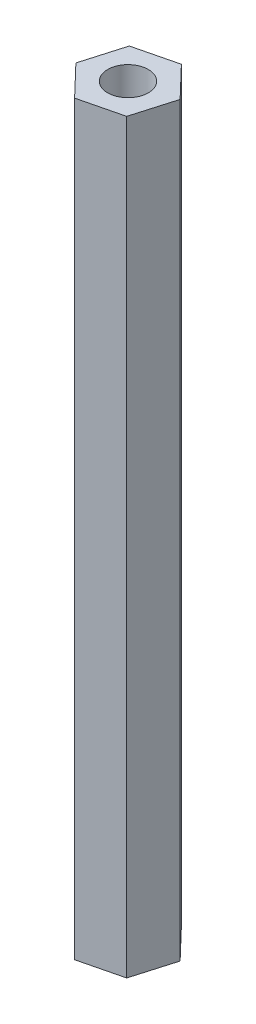
SolidWorks part; units mm, degrees
ref_plane "Front Plane" through (0, 0, 0) normal (0, 0, 1) x (1, 0, 0)
ref_plane "Top Plane" through (0, 0, 0) normal (0, 1, 0) x (1, 0, 0)
ref_plane "Right Plane" through (0, 0, 0) normal (1, 0, 0) x (0, 0, -1)
sketch "Sketch1" plane through (0, 0, 0) normal (0, 1, 0) x (1, 0, 0)
  line L1 (-2.7677, 3.3349) -> (-1.7448, 6.8555)
  line L2 (-1.7448, 6.8555) -> (-4.2822, 9.5017)
  line L3 (-4.2822, 9.5017) -> (-7.8426, 8.6273)
  line L4 (-7.8426, 8.6273) -> (-8.8655, 5.1067)
  line L5 (-8.8655, 5.1067) -> (-6.3281, 2.4605)
  line L6 (-6.3281, 2.4605) -> (-2.7677, 3.3349)
  circle A0 centre (-5.3052, 5.9811) radius 3.175 construction
  dimension "D1" = 6.35
extrude "Boss-Extrude1" add sketch "Sketch1" along normal blind 63.5
sketch "Sketch2" plane through (0, 63.5, 0) normal (0, 1, 0) x (1, 0, 0)
  line L0 (-7.8426, 8.6273) -> (-2.7677, 3.3349) construction
  circle A0 centre (-5.3052, 5.9811) radius 1.7272
  dimension "D1" = 3.4544
extrude "Cut-Extrude1" cut sketch "Sketch2" against normal blind 9.525
sketch "Sketch3" plane through (0, 0, 0) normal (0, -1, 0) x (1, 0, 0)
  line L0 (-4.2822, -9.5017) -> (-6.3281, -2.4605) construction
  circle A0 centre (-5.3052, -5.9811) radius 1.7272
  dimension "D1" = 3.4544
extrude "Cut-Extrude2" cut sketch "Sketch3" against normal blind 9.525
